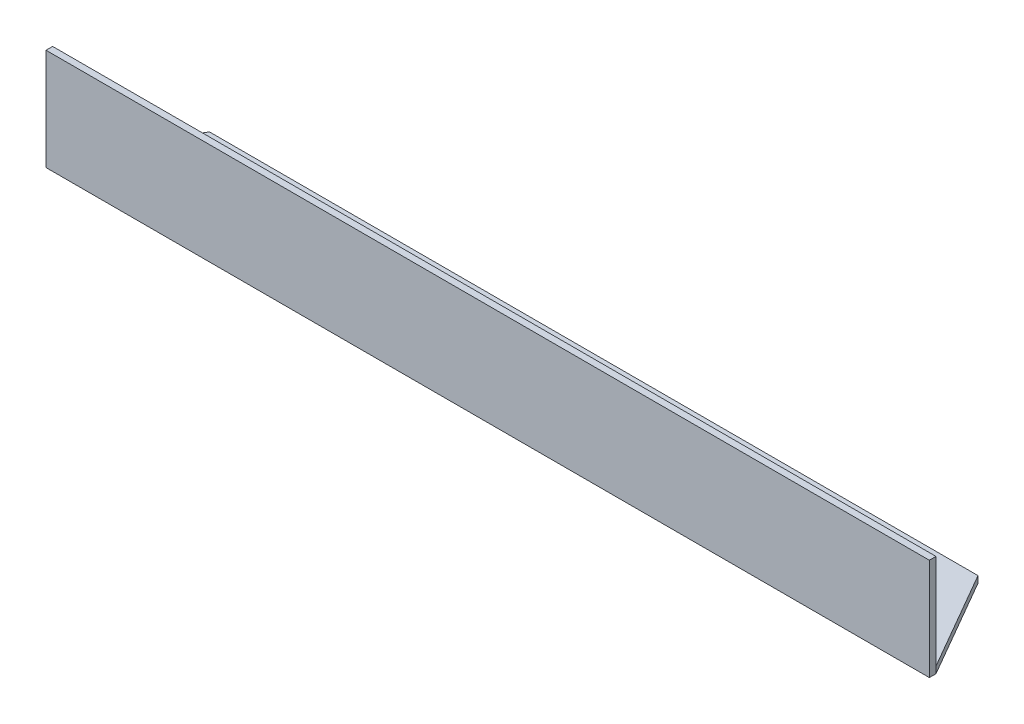
SolidWorks part; units mm, degrees
ref_plane "Front Plane" through (0, 0, 0) normal (0, 0, 1) x (1, 0, 0)
ref_plane "Top Plane" through (0, 0, 0) normal (0, 1, 0) x (1, 0, 0)
ref_plane "Right Plane" through (0, 0, 0) normal (1, 0, 0) x (0, 0, -1)
sketch "Sketch16" plane through (0, 0, 0) normal (0, 1, 0) x (1, 0, 0)
  line L0 (139.2197, 0) -> (126.2232, 22.51) construction
  line L1 (-47.7841, 22.51) -> (126.2232, 22.51)
  line L3 (-60.7803, 0) -> (139.2197, 0)
  line L5 (-60.7803, 0) -> (-47.7841, 22.51) construction
  line L6 (139.2197, 0) -> (126.2232, 22.51)
  line L7 (-47.7841, 22.51) -> (-60.7803, 0)
  line L9 (139.2197, 0) -> (126.2232, 0)
  point P7 (124.2766, 22.21)
sketch "Sketch18" plane through (0, 0, 0) normal (0, 0, 1) x (1, 0, 0)
  line L0 (-60.7803, 0) -> (139.2197, 0) construction
  line L1 (-60.7803, 0) -> (139.2197, 0)
  line L2 (-60.7803, 0) -> (-60.7803, 23.0142)
  line L3 (-60.7803, 23.0142) -> (139.2197, 23.0142)
  line L4 (139.2197, 0) -> (139.2197, 23.0142)
  dimension "D1" = 200
extrude "Boss-Extrude4" add sketch "Sketch18" along normal blind 1.5 contours L4 L3 L2 L1
extrude "Boss-Extrude5" add sketch "Sketch16" along normal blind 1.5 contours L1 L6 L3 L7
